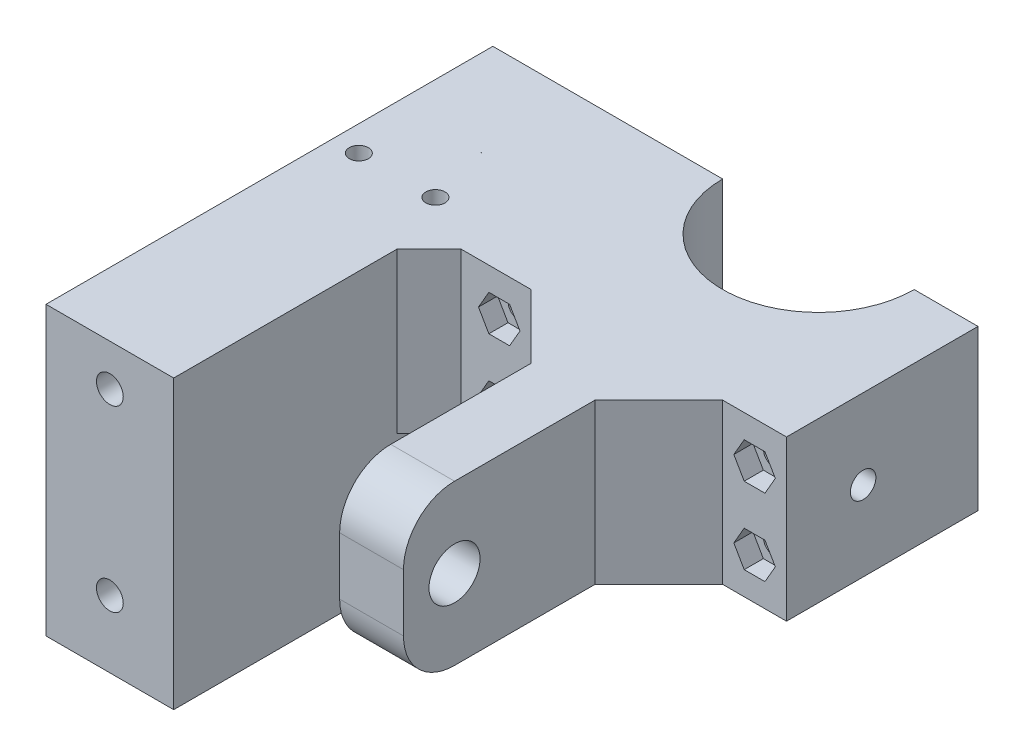
SolidWorks part; units mm, degrees
ref_plane "Спереди" through (0, 0, 0) normal (0, 0, 1) x (1, 0, 0)
ref_plane "Сверху" through (0, 0, 0) normal (0, 1, 0) x (1, 0, 0)
ref_plane "Справа" through (0, 0, 0) normal (1, 0, 0) x (0, 0, -1)
sketch "Sketch1" plane through (0, 0, 0) normal (0, 1, 0) x (1, 0, 0)
  line L0 (26.0276, -8) -> (-23.9724, -8) construction
  line L1 (-13.9724, -8) -> (-23.9724, -8)
  line L2 (-23.9724, -8) -> (-23.9724, -38)
  line L3 (-23.9724, -38) -> (-3.9724, -38)
  line L4 (-3.9724, -38) -> (-3.9724, -78)
  line L5 (-3.9724, -78) -> (6.0276, -78)
  line L6 (6.0276, -78) -> (6.0276, -38)
  line L7 (6.0276, -38) -> (26.0276, -38)
  line L8 (26.0276, -38) -> (26.0276, -8)
  line L9 (16.0276, -8) -> (26.0276, -8)
  circle A0 centre (1.0276, -8) radius 15 construction
  arc A1 (-13.9724, -8) -> (16.0276, -8) centre (1.0276, -8) ccw
  dimension "D2" = 30
  dimension "D1" = 30
  dimension "D3" = 10
  dimension "D4" = 40
  dimension "D5" = 50
extrude "Boss-Extrude1" add sketch "Sketch1" along normal blind 25
sketch "Sketch2" plane through (-3.9724, 0, 0) normal (-1, 0, 0) x (0, 0, 1)
  line L0 (78, 12.5) -> (38, 12.5) construction
  line L1 (78, 25) -> (78, 0) construction
  line L2 (38, 25) -> (38, 0) construction
  circle A0 centre (70, 12.5) radius 4
  dimension "D1" = 8
  dimension "D2" = 8
extrude "Cut-Extrude1" cut sketch "Sketch2" against normal through all
sketch "Sketch3" plane through (0, 0, 8) normal (0, 0, -1) x (-1, 0, 0)
  line L0 (-21.0276, 0) -> (-21.0276, 25) construction
  line L1 (-26.0276, 0) -> (-16.0276, 0) construction
  line L2 (-26.0276, 25) -> (-16.0276, 25) construction
  line L3 (18.9724, 0) -> (18.9724, 25) construction
  line L4 (13.9724, 0) -> (23.9724, 0) construction
  line L5 (13.9724, 25) -> (23.9724, 25) construction
  line L6 (-21.0276, 6.5) -> (18.9724, 6.5) construction
  line L7 (-21.0276, 18.5) -> (18.9724, 18.5) construction
  circle A0 centre (-21.0276, 6.5) radius 1.6
  circle A1 centre (-21.0276, 18.5) radius 1.6
  circle A2 centre (18.9724, 6.5) radius 1.6
  circle A3 centre (18.9724, 18.5) radius 1.6
  point P16 (-21.0276, 12.5)
  dimension "D2" = 3.2
  dimension "D3" = 12
  dimension "D4" = 6
extrude "Cut-Extrude2" cut sketch "Sketch3" against normal through all
sketch "Sketch4" plane through (0, 0, 38) normal (0, 0, 1) x (1, 0, 0)
  line L1 (24.2776, 18.5) -> (22.6526, 21.3146)
  line L2 (22.6526, 21.3146) -> (19.4026, 21.3146)
  line L3 (19.4026, 21.3146) -> (17.7776, 18.5)
  line L4 (17.7776, 18.5) -> (19.4026, 15.6854)
  line L5 (19.4026, 15.6854) -> (22.6526, 15.6854)
  line L6 (22.6526, 15.6854) -> (24.2776, 18.5)
  line L7 (24.2776, 6.5) -> (22.6526, 9.3146)
  line L8 (22.6526, 9.3146) -> (19.4026, 9.3146)
  line L9 (19.4026, 9.3146) -> (17.7776, 6.5)
  line L10 (17.7776, 6.5) -> (19.4026, 3.6854)
  line L11 (19.4026, 3.6854) -> (22.6526, 3.6854)
  line L12 (22.6526, 3.6854) -> (24.2776, 6.5)
  line L13 (-15.7224, 18.5) -> (-17.3474, 21.3146)
  line L14 (-17.3474, 21.3146) -> (-20.5974, 21.3146)
  line L15 (-20.5974, 21.3146) -> (-22.2224, 18.5)
  line L16 (-22.2224, 18.5) -> (-20.5974, 15.6854)
  line L17 (-20.5974, 15.6854) -> (-17.3474, 15.6854)
  line L18 (-17.3474, 15.6854) -> (-15.7224, 18.5)
  line L19 (-15.7224, 6.5) -> (-17.3474, 9.3146)
  line L20 (-17.3474, 9.3146) -> (-20.5974, 9.3146)
  line L21 (-20.5974, 9.3146) -> (-22.2224, 6.5)
  line L22 (-22.2224, 6.5) -> (-20.5974, 3.6854)
  line L23 (-20.5974, 3.6854) -> (-17.3474, 3.6854)
  line L24 (-17.3474, 3.6854) -> (-15.7224, 6.5)
  circle A0 centre (21.0276, 18.5) radius 3.25 construction
  circle A1 centre (21.0276, 6.5) radius 3.25 construction
  circle A2 centre (-18.9724, 18.5) radius 3.25 construction
  circle A3 centre (-18.9724, 6.5) radius 3.25 construction
  dimension "D1" = 6.5
extrude "Cut-Extrude3" cut sketch "Sketch4" against normal blind 3
fillet "Fillet2" radius 8 2 edges at (1.0276, 0, 78) (1.0276, 25, 78)
chamfer "Chamfer2" distance 10 angle 45 2 edges at (6.0276, 12.5, 38) (-3.9724, 12.5, 38)
sketch "Sketch5" plane through (-23.9724, 0, 0) normal (-1, 0, 0) x (0, 0, 1)
  line L0 (8, 12.5) -> (38, 12.5) construction
  line L1 (8, 25) -> (8, 0) construction
  line L2 (38, 25) -> (38, 0) construction
  line L4 (38, 25) -> (8, 25)
  line L5 (38, 25) -> (38, 0)
  line L6 (38, 0) -> (8, 0)
  line L7 (8, 25) -> (8, 0)
  line L8 (38, 25) -> (8, 0) construction
  line L9 (38, 0) -> (8, 25) construction
  point P6 (23, 12.5)
extrude "Boss-Extrude2" add sketch "Sketch5" along normal blind 26
sketch "Sketch6" plane through (0, 0, 38) normal (0, 0, 1) x (1, 0, 0)
  line L0 (-39.9701, 0) -> (-39.9701, 25) construction
  line L1 (-49.9724, 0) -> (-13.9724, 0) construction
  line L2 (-49.9724, 25) -> (-13.9724, 25) construction
  line L4 (-29.9679, 25) -> (-49.9724, 25)
  line L5 (-29.9679, 25) -> (-29.9679, 0)
  line L6 (-29.9679, 0) -> (-49.9724, 0)
  line L7 (-49.9724, 25) -> (-49.9724, 0)
  line L8 (-29.9679, 25) -> (-49.9724, 0) construction
  line L9 (-29.9679, 0) -> (-49.9724, 25) construction
  point P6 (-39.9701, 12.5)
  dimension "D1" = 20.0045
extrude "Boss-Extrude3" add sketch "Sketch6" along normal blind 40
sketch "Sketch7" plane through (0, 0, 0) normal (0, -1, 0) x (1, 0, 0)
  line L0 (-29.9679, 58) -> (-49.9724, 58) construction
  line L1 (-29.9679, 78) -> (-29.9679, 38) construction
  line L2 (-49.9724, 8) -> (-49.9724, 78) construction
  line L3 (-49.9724, 78) -> (-29.9679, 78) construction
  line L4 (-45.1701, 68.2) -> (-34.7701, 68.2)
  line L5 (-45.1701, 68.2) -> (-45.1701, 47.8)
  line L6 (-45.1701, 47.8) -> (-34.7701, 47.8)
  line L7 (-34.7701, 68.2) -> (-34.7701, 47.8)
  line L8 (-45.1701, 68.2) -> (-34.7701, 47.8) construction
  line L9 (-45.1701, 47.8) -> (-34.7701, 68.2) construction
  point P6 (-39.9701, 58)
  dimension "D1" = 10.4
  dimension "D2" = 20.4
  dimension "D3" = 20
extrude "Cut-Extrude4" cut sketch "Sketch7" against normal blind 23
sketch "Sketch9" plane through (0, 0, 0) normal (0, -1, 0) x (1, 0, 0)
  line L0 (-45.1701, 58) -> (-34.7701, 58) construction
  line L1 (-45.1701, 68.2) -> (-45.1701, 47.8) construction
  line L2 (-34.7701, 47.8) -> (-34.7701, 68.2) construction
  line L4 (-49.9724, 78) -> (-29.9679, 78)
  line L5 (-49.9724, 78) -> (-49.9724, 38)
  line L6 (-49.9724, 38) -> (-29.9679, 38)
  line L7 (-29.9679, 78) -> (-29.9679, 38)
  line L8 (-49.9724, 78) -> (-29.9679, 38) construction
  line L9 (-49.9724, 38) -> (-29.9679, 78) construction
  line L10 (-45.1701, 68.2) -> (-34.7701, 68.2)
  line L11 (-45.1701, 68.2) -> (-45.1701, 47.8)
  line L12 (-45.1701, 47.8) -> (-34.7701, 47.8)
  line L13 (-34.7701, 68.2) -> (-34.7701, 47.8)
  line L14 (-45.1701, 68.2) -> (-34.7701, 47.8) construction
  line L15 (-45.1701, 47.8) -> (-34.7701, 68.2) construction
  point P6 (-39.9701, 58)
  point P12 (-39.9701, 58)
extrude "Boss-Extrude4" add sketch "Sketch9" along normal blind 20
sketch "Sketch10" plane through (0, 0, 78) normal (0, 0, 1) x (1, 0, 0)
  line L0 (-39.9701, -20) -> (-39.9701, 25) construction
  line L1 (-29.9679, -20) -> (-49.9724, -20) construction
  line L2 (-29.9679, 25) -> (-49.9724, 25) construction
  circle A0 centre (-39.9701, -9.5) radius 2.1
  circle A1 centre (-39.9701, 18.5) radius 2.1
  point P16 (-39.9701, 2.5)
  dimension "D1" = 28
  dimension "D2" = 4.2
  dimension "D3" = 12
extrude "Cut-Extrude6" cut sketch "Sketch10" against normal through all
chamfer "Chamfer5" distance 5 angle 45 1 edges at (-29.9679, 12.5, 38)
sketch "Sketch11" plane through (26.0276, 0, 0) normal (1, 0, 0) x (0, 0, -1)
  line L0 (-8, 12.5) -> (-38, 12.5) construction
  line L1 (-8, 25) -> (-8, 0) construction
  line L2 (-38, 25) -> (-38, 0) construction
  circle A0 centre (-26, 12.5) radius 2
  dimension "D1" = 4
  dimension "D2" = 18
extrude "Cut-Extrude7" cut sketch "Sketch11" against normal through all
sketch "Sketch12" plane through (0, 0, 38) normal (0, 0, -1) x (-1, 0, 0)
  line L0 (29.9679, -10) -> (49.9724, -10) construction
  line L1 (29.9679, -20) -> (29.9679, 0) construction
  line L2 (49.9724, -20) -> (49.9724, 0) construction
  line L4 (49.9724, -20) -> (29.9679, -20)
  line L5 (49.9724, -20) -> (49.9724, 0)
  line L6 (49.9724, 0) -> (29.9679, 0)
  line L7 (29.9679, -20) -> (29.9679, 0)
  line L8 (49.9724, -20) -> (29.9679, 0) construction
  line L9 (49.9724, 0) -> (29.9679, -20) construction
  circle A0 centre (39.9701, -9.5) radius 2.1
  point P6 (39.9701, -10)
extrude "Boss-Extrude5" add sketch "Sketch12" along normal up to surface (30 mm away) up to face at (-37.8701, 18.5, 8)
sketch "Sketch13" plane through (0, -20, 0) normal (0, -1, 0) x (1, 0, 0)
  line L0 (-29.9679, 33) -> (-49.9724, 33) construction
  line L1 (-29.9679, 8) -> (-29.9679, 78) construction
  line L2 (-49.9724, 78) -> (-49.9724, 8) construction
  line L3 (-49.9724, 8) -> (-29.9679, 8) construction
  circle A0 centre (-33.9701, 33) radius 1.5
  circle A1 centre (-45.9701, 33) radius 1.5
  point P10 (-39.9701, 33)
  dimension "D1" = 3
  dimension "D2" = 12
  dimension "D3" = 6
  dimension "D4" = 25
extrude "Cut-Extrude8" cut sketch "Sketch13" against normal through all
